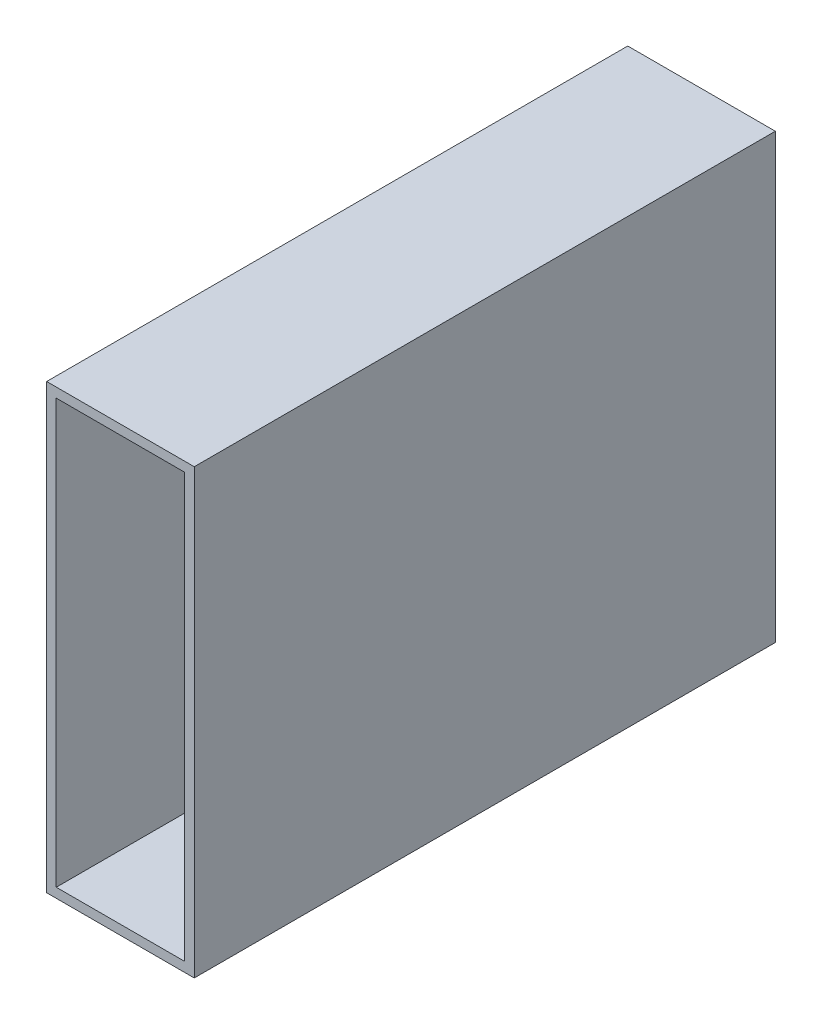
SolidWorks part; units mm, degrees
ref_plane "Front Plane" through (0, 0, 0) normal (0, 0, 1) x (1, 0, 0)
ref_plane "Top Plane" through (0, 0, 0) normal (0, 1, 0) x (1, 0, 0)
ref_plane "Right Plane" through (0, 0, 0) normal (1, 0, 0) x (0, 0, -1)
sketch "Sketch2" plane through (0, 0, 0) normal (0, 0, 1) x (1, 0, 0)
  line L0 (0, 0) -> (0, 38.1)
  line L1 (0, 38.1) -> (12.7, 38.1)
  line L2 (12.7, 38.1) -> (12.7, 0)
  line L3 (12.7, 0) -> (0, 0)
  line L4 (12.7, -38.1) -> (12.7, -36.449)
  line L5 (0, 0) -> (-12.7, 0)
  line L6 (0, 0) -> (0, -38.1)
  line L7 (0, -38.1) -> (-12.7, -38.1)
  line L8 (-12.7, 0) -> (-12.7, -38.1)
  line L9 (-12.7, -38.1) -> (12.7, -38.1)
  line L10 (-12.7, -38.1) -> (-12.7, 38.1)
  line L11 (-12.7, 38.1) -> (12.7, 38.1)
  line L12 (12.7, -38.1) -> (12.7, 38.1)
  line L13 (12.7, -36.449) -> (11.049, -36.449)
  line L14 (-12.7, 38.1) -> (-11.049, 38.1)
  line L15 (-11.049, 38.1) -> (-11.049, 36.449)
  line L17 (-11.049, 36.449) -> (11.049, 36.449)
  line L18 (-11.049, 36.449) -> (-11.049, -36.449)
  line L19 (-11.049, -36.449) -> (11.049, -36.449)
  line L20 (11.049, 36.449) -> (11.049, -36.449)
  dimension "D1" = 38.1
  dimension "D2" = 12.7
  dimension "D3" = 38.1
  dimension "D4" = 12.7
  dimension "D5" = 1.651
  dimension "D6" = 1.651
  dimension "D7" = 1.651
  dimension "D8" = 1.651
extrude "Boss-Extrude1" add sketch "Sketch2" along normal blind 100 contours L18 L15 L11 L10 L5 | L15 L17 L0 L11 | L17 L20 L3 L2 L1 L0 | L3 L20 L13 L12 | L19 L18 L5 L8 L7 L6 | L19 L6 L9 L4 L13
equation "\"D3@Sketch2\"=\"D1@Sketch2\""
equation "\"D4@Sketch2\"=\"D2@Sketch2\""
